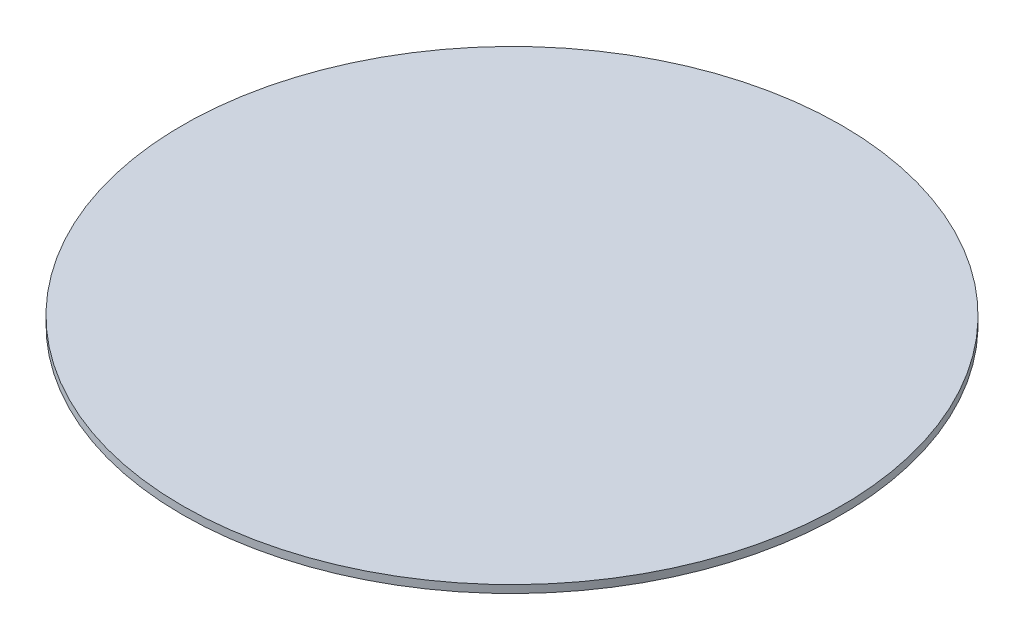
SolidWorks part; units mm, degrees
ref_plane "Ebene vorne" through (0, 0, 0) normal (0, 0, 1) x (1, 0, 0)
ref_plane "Ebene oben" through (0, 0, 0) normal (0, 1, 0) x (1, 0, 0)
ref_plane "Ebene rechts" through (0, 0, 0) normal (1, 0, 0) x (0, 0, -1)
sketch "Skizze1" plane through (0, 0, 0) normal (0, 1, 0) x (1, 0, 0)
  circle A0 centre (0, 0) radius 850
  dimension "Breite" = 1700
extrude "Aufsatz-Linear austragen1" add sketch "Skizze1" along normal blind 20
equation "\"Staerke@Aufsatz-Linear austragen1\" = ( if ( \"Breite@Skizze1\" = 1600 , 12 , 1000 ) )"
